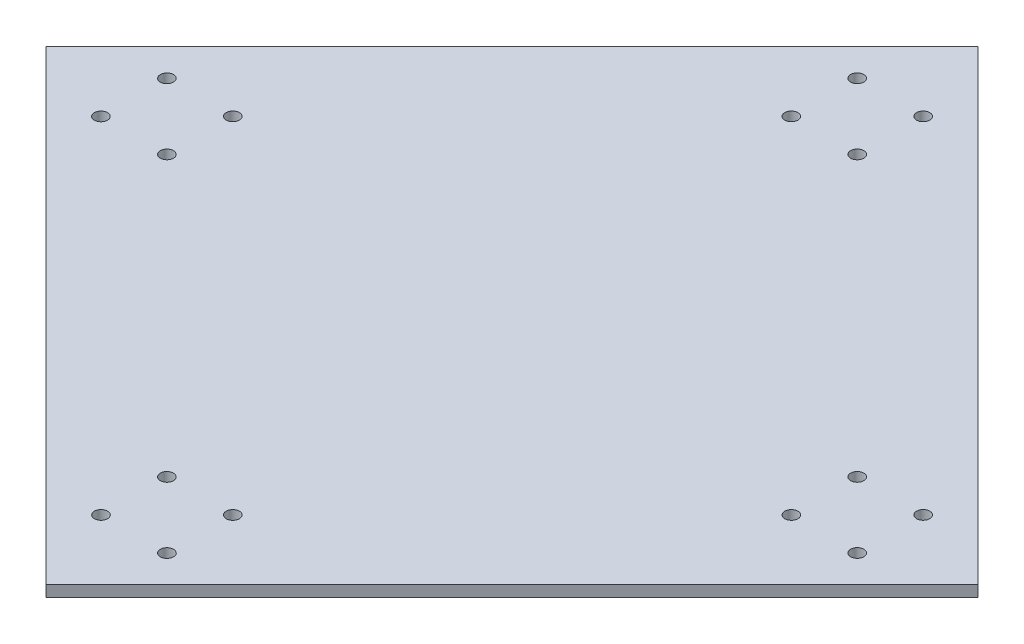
SolidWorks part; units mm, degrees
ref_plane "Front Plane" through (0, 0, 0) normal (0, 0, 1) x (1, 0, 0)
ref_plane "Top Plane" through (0, 0, 0) normal (0, 1, 0) x (1, 0, 0)
ref_plane "Right Plane" through (0, 0, 0) normal (1, 0, 0) x (0, 0, -1)
sketch "Sketch3" plane through (0, 0, 0) normal (0, 1, 0) x (1, 0, 0)
  line L0 (-20787.2475, 82043.6963) -> (260209.1191, 82043.6963) construction
  line L1 (-11608.6225, 82043.6963) -> (94457.3926, 188109.7135)
  line L2 (-11608.6225, 82043.6963) -> (94472.1693, -24037.0955)
  line L3 (94472.1693, -24037.0955) -> (200523.4098, 82043.6963)
  line L4 (94457.3926, 188109.7135) -> (200523.4098, 82043.6963)
  line L5 (94472.1693, 212458.6987) -> (94472.1693, -55401.6589) construction
  line L6 (31440.0954, 168109.7135) -> (166638.0807, 168109.7135) construction
  line L7 (31440.0954, 153109.7135) -> (166638.0807, 153109.7135) construction
  line L8 (86972.1693, 173134.9572) -> (86972.1693, 141299.0948) construction
  line L9 (101972.1693, 173134.9572) -> (101972.1693, 141299.0948) construction
  circle A0 centre (86957.3947, 168109.7135) radius 1500
  circle A1 centre (101972.1693, 168109.7135) radius 1500
  circle A2 centre (101972.1693, 153109.7135) radius 1500
  circle A3 centre (86972.1693, 153109.7135) radius 1500
  circle A4 centre (165538.1865, 74543.6963) radius 1500
  circle A5 centre (86972.1693, 10977.6792) radius 1500
  circle A6 centre (23406.1521, 89543.6963) radius 1500
  circle A7 centre (180538.1865, 89558.4709) radius 1500
  circle A8 centre (180538.1865, 74543.6963) radius 1500
  circle A9 centre (165538.1865, 74543.6963) radius 1500
  circle A10 centre (165538.1865, 89543.6963) radius 1500
  circle A11 centre (101986.9439, -4022.3208) radius 1500
  circle A12 centre (86972.1693, -4022.3208) radius 1500
  circle A13 centre (86972.1693, 10977.6792) radius 1500
  circle A14 centre (101972.1693, 10977.6792) radius 1500
  circle A15 centre (8406.1521, 74528.9217) radius 1500
  circle A16 centre (8406.1521, 89543.6963) radius 1500
  circle A17 centre (23406.1521, 89543.6963) radius 1500
  circle A18 centre (23406.1521, 74543.6963) radius 1500
  point P33 (94472.1693, 82043.6963)
  point P58 (94472.1693, 82043.6963)
  dimension "D11" = 3000
  dimension "D12" = 3000
  dimension "D13" = 3000
  dimension "D14" = 3000
  dimension "D1" = 150000
  dimension "D2" = 150000
  dimension "D3" = 135197.9853
  dimension "D4" = 135197.9853
  dimension "D5" = 280996.3666
  dimension "D6" = 267860.3576
  dimension "D7" = 15000
  dimension "D8" = 20000
  dimension "D9" = 7500
  dimension "D10" = 7500
  dimension "D15" = 4
  dimension "D16" = 4
extrude "Boss-Extrude2" add sketch "Sketch3" along normal blind 2500 contours L4 L1 L2 L3 A18 A16 A15 A14 A12 A11 A10 A8 A7 A6 A5 A4 A3 A2 A1 A0
